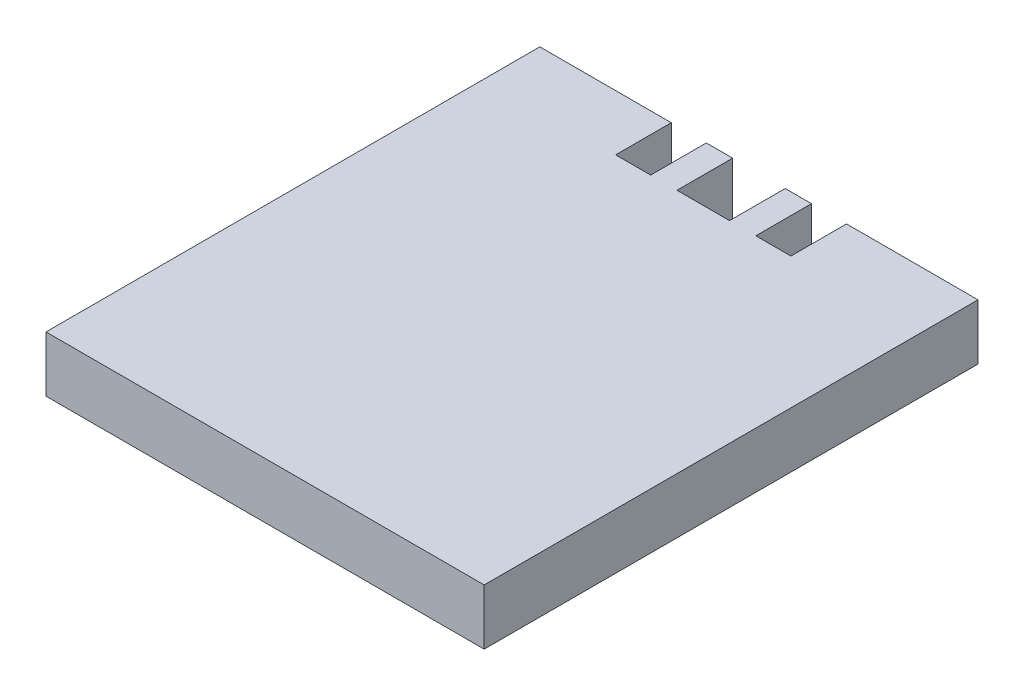
SolidWorks part; units mm, degrees
ref_plane "Front Plane" through (0, 0, 0) normal (0, 0, 1) x (1, 0, 0)
ref_plane "Top Plane" through (0, 0, 0) normal (0, 1, 0) x (1, 0, 0)
ref_plane "Right Plane" through (0, 0, 0) normal (1, 0, 0) x (0, 0, -1)
sketch "Sketch1" plane through (0, 0, 0) normal (0, 1, 0) x (1, 0, 0)
  line L0 (12.5, 0) -> (12.5, 25) construction
  line L1 (0, 0) -> (25, 0)
  line L2 (0, 0) -> (0, 25)
  line L3 (7.5, 25) -> (9.5, 25)
  line L4 (25, 0) -> (25, 25)
  line L5 (11, 25) -> (11, 28.175)
  line L6 (11, 28.175) -> (9.5, 28.175)
  line L7 (9.5, 28.175) -> (9.5, 25)
  line L8 (7.5, 25) -> (7.5, 28.175)
  line L9 (7.5, 28.175) -> (0, 28.175)
  line L10 (0, 28.175) -> (0, 25)
  line L11 (14, 25) -> (14, 28.175)
  line L12 (14, 28.175) -> (15.5, 28.175)
  line L13 (15.5, 28.175) -> (15.5, 25)
  line L14 (17.5, 25) -> (17.5, 28.175)
  line L15 (25, 28.175) -> (25, 25)
  line L16 (17.5, 28.175) -> (25, 28.175)
  line L17 (15.5, 25) -> (17.5, 25)
  line L18 (11, 25) -> (12.5, 25)
  line L19 (0, 25) -> (11, 25) construction
  line L20 (14, 25) -> (25, 25) construction
  line L21 (12.5, 25) -> (14, 25)
  dimension "D1" = 25
  dimension "D2" = 25
  dimension "D3" = 3.175
  dimension "D4" = 1.5
  dimension "D5" = 1.5
  dimension "D6" = 5
  dimension "D7" = 3.175
extrude "Boss-Extrude1" add sketch "Sketch1" along normal blind 3.175
